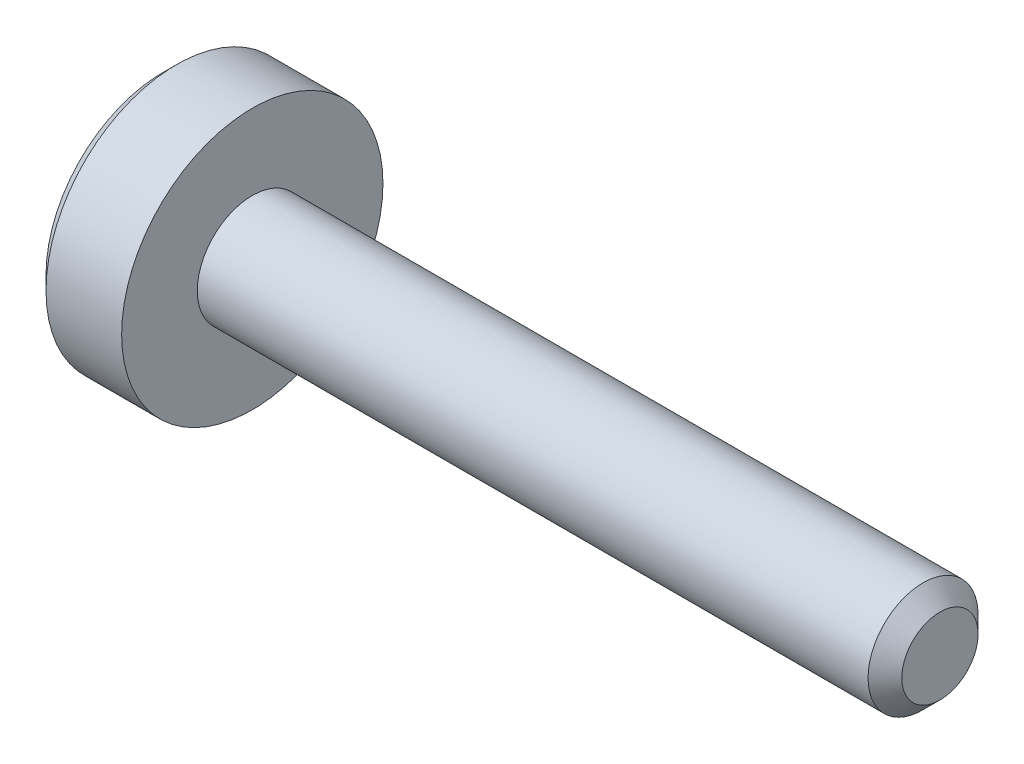
SolidWorks part; units mm, degrees
material "AISI 304"
ref_plane "正面" through (0, 0, 0) normal (0, 0, 1) x (1, 0, 0)
ref_plane "平面" through (0, 0, 0) normal (0, 1, 0) x (1, 0, 0)
ref_plane "右側面" through (0, 0, 0) normal (1, 0, 0) x (0, 0, -1)
ref_plane "Plane1" through (0, 0, 0) normal (0, 0, 1) x (1, 0, 0)
sketch "Sketch1" plane through (0, 0, 0) normal (0, 0, 1) x (1, 0, 0)
  line L0 (-1.3, 0) -> (-1.3, 1.7)
  line L1 (-1.3, 1.7) -> (-1.1, 1.9)
  line L2 (-1.1, 1.9) -> (0, 1.9)
  line L3 (0, 1.9) -> (0, 0.8)
  line L4 (0, 0.8) -> (9.7545, 0.8)
  line L5 (9.7545, 0.8) -> (10, 0.5545)
  line L6 (10, 0.5545) -> (10, 0)
  line L7 (10, 0) -> (-1.3, 0)
  line L8 (10, 0) -> (-1.3, 0) construction
  dimension "D1" = 0.8
revolve "Revolve1" add sketch "Sketch1" angle 360 about L8
cosmetic thread "Cosmetic Thread1" parameters "D1"=9.5748, "D2"=1.509
ref_plane "Plane2" through (-1.3, 0, 0) normal (1, 0, 0) x (0, 0, -1)
sketch "Sketch2" plane through (-1.3, 0, 0) normal (1, 0, 0) x (0, 0, -1)
  line L0 (-0.65, -0.3753) -> (0, -0.7506)
  line L1 (0, -0.7506) -> (0.65, -0.3753)
  line L2 (0.65, -0.3753) -> (0.65, 0.3753)
  line L3 (0.65, 0.3753) -> (0, 0.7506)
  line L4 (0, 0.7506) -> (-0.65, 0.3753)
  line L5 (-0.65, 0.3753) -> (-0.65, -0.3753)
extrude "Cut-Extrude1" cut sketch "Sketch2" along normal blind 0.7
